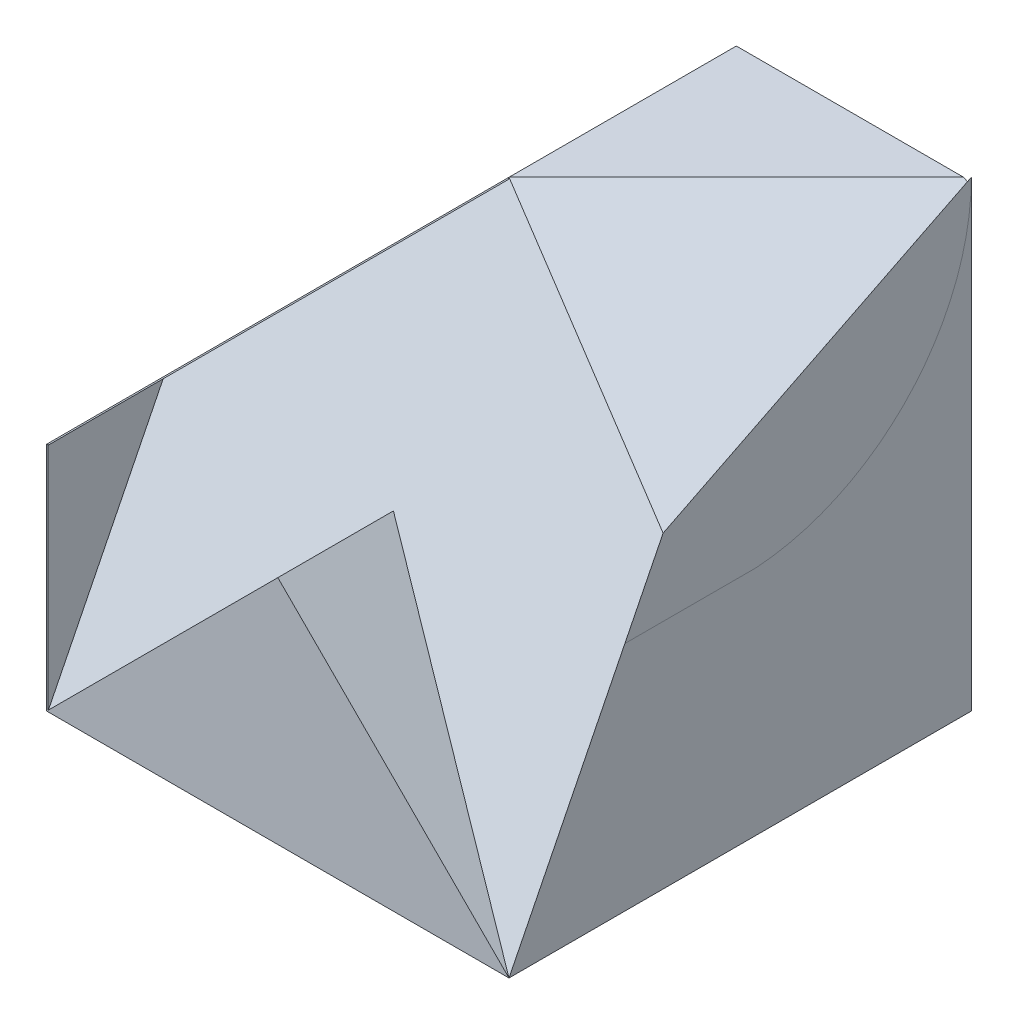
SolidWorks part; units mm, degrees
ref_plane "Front Plane" through (0, 0, 0) normal (0, 0, 1) x (1, 0, 0)
ref_plane "Top Plane" through (0, 0, 0) normal (0, 1, 0) x (1, 0, 0)
ref_plane "Right Plane" through (0, 0, 0) normal (1, 0, 0) x (0, 0, -1)
sketch "Sketch1" plane through (0, 0, 0) normal (0, 0, 1) x (1, 0, 0)
  line L1 (0, 0) -> (60, 0)
  line L2 (0, 0) -> (0, 60)
  line L3 (0, 60) -> (60, 60)
  line L4 (60, 0) -> (60, 60)
  dimension "D1" = 60
  dimension "D2" = 60
extrude "Boss-Extrude1" add sketch "Sketch1" along normal blind 60
sketch "Sketch2" plane through (0, 0, 60) normal (0, 0, 1) x (1, 0, 0)
  line L0 (30, 60) -> (0, 30)
  line L1 (60, 60) -> (0, 60) construction
  line L2 (0, 60) -> (0, 0) construction
  line L3 (0, 30) -> (0, 60)
  line L4 (0, 60) -> (30, 60)
extrude "Cut-Extrude1" cut sketch "Sketch2" against normal blind 60
sketch "Sketch3" plane through (60, 0, 0) normal (1, 0, 0) x (0, 0, -1)
  line L0 (-30, 60) -> (-60, 30)
  line L1 (-60, 60) -> (0, 60) construction
  line L2 (-60, 0) -> (-60, 60) construction
  line L3 (-60, 30) -> (-60, 60)
  line L4 (-60, 60) -> (-30, 60)
  line L5 (-30, 60) -> (-29.5965, 59.8897)
  line M2 (0, 60) -> (-60, 60)
  line M3 (-60, 60) -> (-60, 0)
extrude "Cut-Extrude2" cut sketch "Sketch3" against normal blind 60 contours L0 M2 M3
ref_plane "Plane1" through (30, 60, 30) normal (0.4082, 0.8165, 0.4082) x (0.9129, -0.3651, -0.1826)
sketch "Sketch4" plane through (30, 60, 30) normal (0.4082, 0.8165, 0.4082) x (0.9129, -0.3651, -0.1826)
  line L0 (0, 0) -> (32.8634, 26.8328)
  line L1 (32.8634, 26.8328) -> (32.8634, -40.2492)
  line L2 (32.8634, -40.2492) -> (0, 0)
extrude "Cut-Extrude3" cut sketch "Sketch4" along normal blind 60
ref_plane "Plane2" through (0, 24, 48) normal (0, 0.4472, 0.8944) x (1, 0, 0)
sketch "Sketch5" plane through (0, 24, 48) normal (0, 0.4472, 0.8944) x (1, 0, 0)
  line L0 (30, 40.2492) -> (0, -26.8328)
  line L1 (0, -26.8328) -> (60, -26.8328)
  line L2 (60, -26.8328) -> (30, 40.2492)
  line L3 (30, 40.2492) -> (30.4234, 39.719)
extrude "Cut-Extrude4" cut sketch "Sketch5" along normal blind 60 contours L1 L2 L0
sketch "Sketch6" plane through (10, -4, 2) normal (0.9129, -0.3651, 0.1826) x (0.1695, -0.0678, -0.9832)
  line L0 (-58.9915, 32.311) -> (-58.9915, 0)
  line L1 (-58.9915, 0) -> (-28.4787, 66.8503)
  line L2 (-28.4787, 66.8503) -> (-58.9915, 32.311)
extrude "Cut-Extrude5" cut sketch "Sketch6" against normal blind 60
sketch "Sketch7" plane through (40, 16, -8) normal (-0.9129, -0.3651, 0.1826) x (0.1695, 0.0678, 0.9832)
  line L0 (38.6496, 44.5669) -> (69.1625, -22.2834)
  line L1 (69.1625, -22.2834) -> (69.1625, 10.0275)
  line L2 (69.1625, 10.0275) -> (38.6496, 44.5669)
extrude "Cut-Extrude6" cut sketch "Sketch7" against normal blind 60
sketch "Sketch8" plane through (11.7241, 4.6897, 68) normal (-0.1695, -0.0678, -0.9832) x (-0.9855, 0.0117, 0.1691)
  line L0 (-36.8086, 25.8008) -> (-47.0823, 27.8003)
  line L1 (-47.0823, 27.8003) -> (-48.9848, 27.0171)
  line L2 (-48.9848, 27.0171) -> (-48.9848, -4.1281)
  line L3 (-48.9848, -4.1281) -> (-48.9848, 27.0171) construction
  line L4 (-48.9848, -4.1281) -> (-36.8086, 25.8008) construction
  line L5 (-48.9848, -4.1281) -> (-36.8086, 25.8008)
extrude "Cut-Extrude7" cut sketch "Sketch8" against normal blind 60
sketch "Sketch9" plane through (-10, 4, 58) normal (0.1695, -0.0678, -0.9832) x (-0.9855, -0.0117, -0.1691)
  line L0 (-10.1469, -4.1281) -> (-10.1469, 25.9431)
  line L1 (-10.1469, 25.9431) -> (-12.0494, 27.8003)
  line L2 (-12.0494, 27.8003) -> (-22.3231, 25.8008)
  line L3 (-22.3231, 25.8008) -> (-10.1469, -4.1281)
extrude "Cut-Extrude8" cut sketch "Sketch9" against normal blind 60
ref_plane "Plane3" through (0, 0, 60) normal (0, 0, 1) x (1, 0, 0)
sketch "Sketch11" plane through (0, 0, 60) normal (0, 0, 1) x (1, 0, 0)
  line L0 (0, 0) -> (30, 30)
  line L1 (30, 30) -> (60, 0)
  line L2 (60, 0) -> (0, 0)
  dimension "D1" = 30
  dimension "D2" = 30
extrude "Boss-Extrude3" add sketch "Sketch11" against normal blind 60
sketch "Sketch12" plane through (0, 0, 0) normal (-1, 0, 0) x (0, 0, 1)
  line L0 (45, 30) -> (60, 0)
  line L1 (60, 0) -> (60, 30)
  line L2 (60, 30) -> (45, 30)
extrude "Boss-Extrude7" add sketch "Sketch12" against normal blind 0.15
sketch "Sketch13" plane through (-15, 15, 0) normal (-0.7071, 0.7071, 0) x (0.7071, 0.7071, 0)
  line L0 (63.6396, -30) -> (21.2132, -60)
  line L1 (21.2132, -60) -> (21.2132, -45)
  line L2 (21.2132, -45) -> (63.6396, -30)
extrude "Boss-Extrude8" add sketch "Sketch13" against normal blind 0.15
sketch "Sketch14" plane through (0, 0, 0) normal (0, 0, -1) x (-1, 0, 0)
  line L0 (-30, 30) -> (0, 30)
  line L1 (0, 30) -> (-30, 60)
  line L2 (-30, 60) -> (-60, 60)
  arc A0 (-60, 60) -> (-30, 30) centre (-30, 60) ccw
extrude "Cut-Extrude10" cut sketch "Sketch14" against normal blind 0.5
sketch "Sketch15" plane through (60, 0, 0) normal (1, 0, 0) x (0, 0, -1)
  line L0 (-27.8904, 30.0743) -> (-44.9629, 30.0743)
  line L1 (-40, 40) -> (-60, 0) construction
  line L2 (-44.9629, 30.0743) -> (-40, 40)
  line L3 (-40, 40) -> (0, 60)
  arc A0 (0, 60) -> (-27.8904, 30.0743) centre (-30, 60) cw
  dimension "D1" = 30
  dimension "D2" = 30
  dimension "D3" = 17.0725
extrude "Boss-Extrude10" add sketch "Sketch15" along normal blind 0.0001
